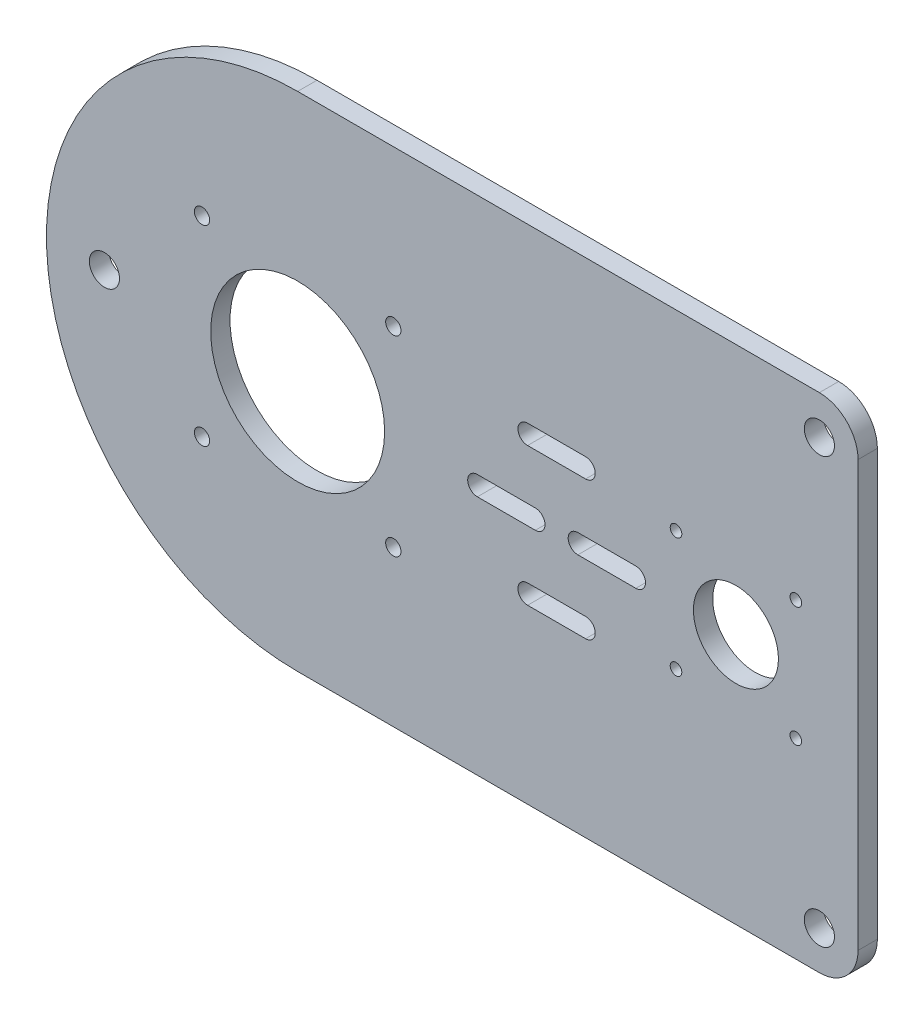
SolidWorks part; units mm, degrees
ref_plane "Front Plane" through (0, 0, 0) normal (0, 0, 1) x (1, 0, 0)
ref_plane "Top Plane" through (0, 0, 0) normal (0, 1, 0) x (1, 0, 0)
ref_plane "Right Plane" through (0, 0, 0) normal (1, 0, 0) x (0, 0, -1)
sketch "Sketch1" plane through (0, 0, 0) normal (0, 0, 1) x (1, 0, 0)
  line L0 (-105, 0) -> (105, 0) construction
  line L3 (-40, -65) -> (95, -65)
  line L4 (105, 55) -> (105, -55)
  line L5 (-40, 65) -> (95, 65)
  line L6 (73.4, 0) -> (73.4, 19.4035) construction
  line L7 (-40, 72.5348) -> (-40, -130.0221) construction
  line L8 (27, 17.578) -> (27, -21.4066) construction
  line L9 (32.5, 2.4) -> (47.5, 2.4)
  line L10 (47.5, -2.6) -> (32.5, -2.6)
  line L11 (19.5, 20.4) -> (34.5, 20.4)
  line L12 (34.5, 15.4) -> (19.5, 15.4)
  line L13 (21.5, 2.4) -> (6.5, 2.4)
  line L14 (6.5, -2.6) -> (21.5, -2.6)
  line L15 (34.5, -15.4) -> (19.5, -15.4)
  line L16 (19.5, -20.4) -> (34.5, -20.4)
  circle A0 centre (95, 55) radius 3.9
  circle A1 centre (95, -55) radius 3.9
  arc A2 (-40, 65) -> (-40, -65) centre (-40, 0) ccw
  circle A3 centre (-90, 0) radius 3.9
  arc A4 (95, -65) -> (105, -55) centre (95, -55) ccw
  arc A5 (95, 65) -> (105, 55) centre (95, 55) cw
  circle A6 centre (-40, 0) radius 22.5
  circle A7 centre (-64.75, 24.75) radius 1.975
  circle A8 centre (-15.25, 24.75) radius 1.975
  circle A9 centre (-15.25, -24.75) radius 1.975
  circle A10 centre (-64.75, -24.75) radius 1.975
  circle A11 centre (73.4, 0) radius 11
  circle A12 centre (57.9, 15.5) radius 1.5
  circle A13 centre (88.9, 15.5) radius 1.5
  circle A14 centre (88.9, -15.5) radius 1.5
  circle A15 centre (57.9, -15.5) radius 1.5
  arc A16 (47.5, 2.4) -> (47.5, -2.6) centre (47.5, -0.1) cw
  arc A17 (32.5, 2.4) -> (32.5, -2.6) centre (32.5, -0.1) ccw
  arc A18 (34.5, 20.4) -> (34.5, 15.4) centre (34.5, 17.9) cw
  arc A19 (19.5, 20.4) -> (19.5, 15.4) centre (19.5, 17.9) ccw
  arc A20 (21.5, 2.4) -> (21.5, -2.6) centre (21.5, -0.1) cw
  arc A21 (6.5, 2.4) -> (6.5, -2.6) centre (6.5, -0.1) ccw
  arc A22 (19.5, -20.4) -> (19.5, -15.4) centre (19.5, -17.9) cw
  arc A23 (34.5, -20.4) -> (34.5, -15.4) centre (34.5, -17.9) ccw
  point P0 (0, 0)
  point P19 (105, -65)
  point P22 (105, 65)
  point P57 (40, 2.4)
  dimension "D3" = 7.8
  dimension "D7" = 65
  dimension "D6" = 40
  dimension "D8" = 50
  dimension "D4" = 105
  dimension "D5" = 10
  dimension "D9" = 110
  dimension "D10" = 45
  dimension "D11" = 3.95
  dimension "D14" = 22
  dimension "D16" = 3
  dimension "D19" = 67
  dimension "D21" = 2.5
  dimension "D24" = 2.5
  dimension "D1" = 65
  dimension "D2" = 65
  dimension "D12" = 24.75
  dimension "D13" = 24.75
  dimension "D15" = 113.4
  dimension "D17" = 15.5
  dimension "D18" = 15.5
  dimension "D20" = 15
  dimension "D22" = 2.4
  dimension "D23" = 15
  dimension "D25" = 7.5
  dimension "D26" = 17.9
  dimension "D27" = 13
extrude "Boss-Extrude3" add sketch "Sketch1" along normal blind 5
